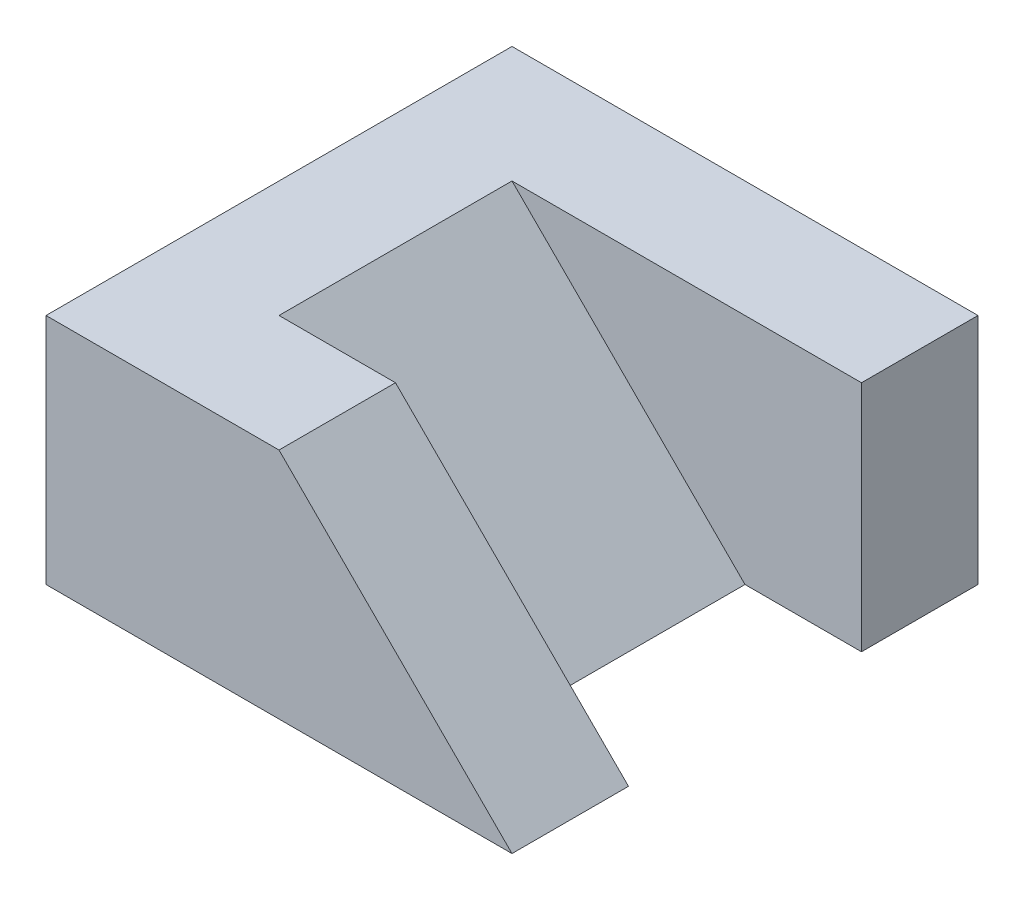
SolidWorks part; units mm, degrees
ref_plane "前基準面" through (0, 0, 0) normal (0, 0, 1) x (1, 0, 0)
ref_plane "上基準面" through (0, 0, 0) normal (0, 1, 0) x (1, 0, 0)
ref_plane "右基準面" through (0, 0, 0) normal (1, 0, 0) x (0, 0, -1)
sketch "草圖1" plane through (0, 0, 0) normal (0, 1, 0) x (1, 0, 0)
  line L1 (10, 10) -> (-10, 10)
  line L2 (10, 10) -> (10, -10)
  line L3 (10, -10) -> (-10, -10)
  line L4 (-10, 10) -> (-10, -10)
  line L5 (10, 10) -> (-10, -10) construction
  line L6 (10, -10) -> (-10, 10) construction
  line L7 (10, 5) -> (5, 5)
  line L8 (10, 5) -> (10, -5)
  line L9 (10, -5) -> (5, -5)
  line L10 (5, 5) -> (5, -5)
  point P0 (0, 0)
  dimension "D1" = 20
  dimension "D2" = 20
  dimension "D3" = 5
  dimension "D4" = 5
  dimension "D5" = 10
extrude "填料-伸長1" add sketch "草圖1" along normal blind 10 contours L10 L7 L2 L1 L4 L3 L9
sketch "草圖2" plane through (0, 0, 10) normal (0, 0, 1) x (1, 0, 0)
  line L1 (10, 10) -> (-10, 10) construction
  line L2 (10, 10) -> (10, 0) construction
  line L3 (10, 0) -> (10, 10)
  line L4 (10, 10) -> (-5, 10)
  line L5 (-5, 10) -> (5, 0)
  line L6 (10, 0) -> (-10, 0) construction
  line L7 (5, 0) -> (10, 0)
  dimension "D1" = 5
  dimension "D2" = 5
extrude "除料-伸長1" cut sketch "草圖2" against normal blind 10 from offset 5 offset against normal yes
sketch "草圖3" plane through (0, 0, 10) normal (0, 0, 1) x (1, 0, 0)
  line L0 (0, 10) -> (10, 0)
  line L1 (10, 10) -> (-10, 10) construction
  line L2 (10, 0) -> (10, 10)
  line L3 (10, 10) -> (0, 10)
  dimension "D1" = 10
extrude "除料-伸長2" cut sketch "草圖3" against normal blind 5
scale "縮放比例1" scale about centroid uniform scaling yes scale factor 0.2
